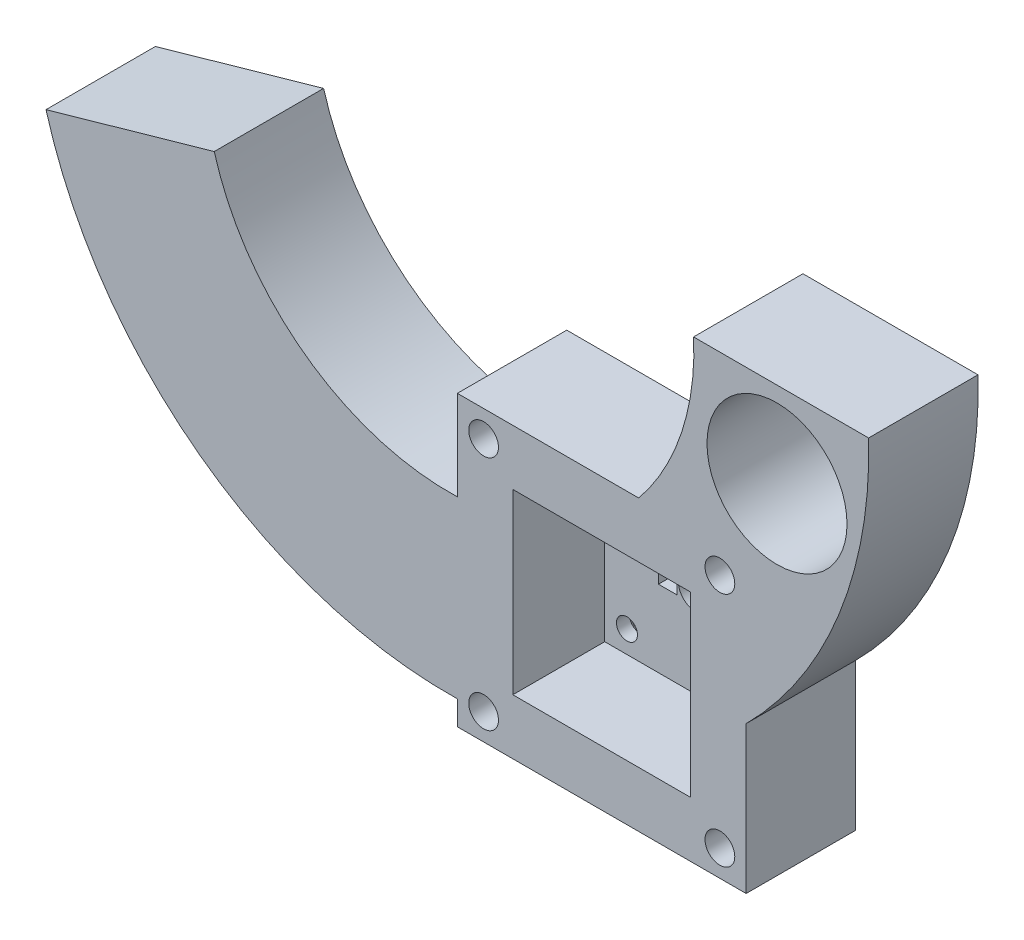
SolidWorks part; units mm, degrees
ref_plane "Plan de face" through (0, 0, 0) normal (0, 0, 1) x (1, 0, 0)
ref_plane "Plan de dessus" through (0, 0, 0) normal (0, 1, 0) x (1, 0, 0)
ref_plane "Plan de droite" through (0, 0, 0) normal (1, 0, 0) x (0, 0, -1)
sketch "Esquisse1" plane through (0, 0, 0) normal (0, 0, 1) x (1, 0, 0)
  line L0 (-16.5, 16.5) -> (16.5, -16.5) construction
  line L1 (-16.5, 16.5) -> (16.5, 16.5)
  line L2 (-16.5, 16.5) -> (-16.5, -16.5)
  line L3 (-16.5, -16.5) -> (16.5, -16.5)
  line L4 (16.5, 16.5) -> (16.5, -16.5)
  line L5 (-16.5, -16.5) -> (16.5, 16.5) construction
  line L11 (10.6664, -10.6664) -> (-10.6664, 10.6664) construction
  line L12 (10.6664, 10.6664) -> (-10.6664, -10.6664) construction
  point P4 (0, 0)
  point P5 (0, 0)
  dimension "D1" = 33
  dimension "D2" = 33
  dimension "D3" = 16.5
  dimension "D4" = 16.5
extrude "Boss.-Extru.1" add sketch "Esquisse1" along normal blind 12.5
sketch "Esquisse2" plane through (0, 0, 12.5) normal (0, 0, 1) x (1, 0, 0)
  line L0 (-16.5, 16.5) -> (16.5, -16.5) construction
  line L1 (-16.5, -16.5) -> (16.5, 16.5) construction
  line L2 (-10.16, 0) -> (10.16, 0) construction
  line L3 (10.16, -10.16) -> (-10.16, -10.16) construction
  line L4 (-16.5, 16.5) -> (-16.5, -16.5)
  line L5 (-16.5, -16.5) -> (16.5, -16.5)
  line L6 (16.5, -16.5) -> (16.5, 16.5)
  line L7 (16.5, 16.5) -> (-16.5, 16.5)
  line L8 (-16.5, 16.5) -> (-16.5, -16.5)
  line L9 (-16.5, -16.5) -> (16.5, -16.5)
  line L10 (16.5, -16.5) -> (16.5, 16.5)
  line L11 (16.5, 16.5) -> (-16.5, 16.5)
  line L12 (10.16, -10.16) -> (10.16, 10.16) construction
  line L13 (10.16, 10.16) -> (-10.16, 10.16) construction
  line L14 (-10.16, -10.16) -> (-10.16, 10.16) construction
  line L15 (10.16, -10.16) -> (-10.16, 10.16) construction
  line L16 (10.16, 10.16) -> (-10.16, -10.16) construction
  line L17 (10.16, -10.16) -> (-10.16, -10.16)
  line L18 (10.16, -10.16) -> (10.16, 10.16)
  line L19 (10.16, 10.16) -> (-10.16, 10.16)
  line L20 (-10.16, -10.16) -> (-10.16, 10.16)
  line L21 (10.16, -10.16) -> (-10.16, 10.16) construction
  line L22 (10.16, 10.16) -> (-10.16, -10.16) construction
  line L23 (-7.62, 8.82) -> (7.62, 8.82)
  line L24 (7.62, 8.82) -> (7.62, 6.42)
  line L25 (7.62, 6.42) -> (-7.62, 6.42)
  circle A0 centre (-7.62, 7.62) radius 1.2
  circle A1 centre (7.62, 7.62) radius 1.2
  circle A2 centre (7.62, -7.62) radius 1.2
  circle A3 centre (-7.62, -7.62) radius 1.2
  point P2 (0, 0)
  point P10 (7.62, 7.62)
  point P11 (-7.62, 7.62)
  point P16 (0, 0)
  dimension "D8" = 2.4
  dimension "D9" = 2.4
  dimension "D10" = 2.4
  dimension "D2" = 20.32
  dimension "D3" = 20.32
  dimension "D4" = 2.54
  dimension "D5" = 2.54
  dimension "D6" = 2.54
  dimension "D7" = 2.54
  dimension "D1" = 0
sketch "Esquisse3" plane through (0, 0, 12.5) normal (0, 0, 1) x (1, 0, 0)
  line L0 (-0.95, 1.7) -> (1.45, -1.7) construction
  line L1 (-4.02, 1.4) -> (-1.92, 1.4)
  line L2 (-4.02, 1.4) -> (-4.02, -1.4)
  line L3 (-4.02, -1.4) -> (-1.92, -1.4)
  line L4 (-1.92, 1.4) -> (-1.92, -1.4)
  line L5 (-0.95, 1.7) -> (1.45, 1.7)
  line L6 (-0.95, 1.7) -> (-0.95, -1.7)
  line L7 (-0.95, -1.7) -> (1.45, -1.7)
  line L8 (1.45, 1.7) -> (1.45, -1.7)
  line L9 (-0.95, -1.7) -> (1.45, 1.7) construction
  line L10 (-4.02, 1.4) -> (-1.92, -1.4) construction
  line L11 (-4.02, -1.4) -> (-1.92, 1.4) construction
  line L12 (10.16, -10.16) -> (10.16, 10.16) construction
  circle A0 centre (0.25, 0) radius 2
  point P8 (0.25, 0)
  point P9 (-2.97, 0)
  dimension "D7" = 4
  dimension "D1" = 3.22
  dimension "D2" = 9.91
  dimension "D3" = 2.8
  dimension "D4" = 2.1
  dimension "D5" = 3.4
  dimension "D6" = 2.4
extrude "Enlèv. mat.-Extru.1" cut sketch "Esquisse3" against normal through all contours L1 L4 L3 L2 | A0
sketch "Esquisse4" plane through (0, 0, 12.5) normal (0, 0, 1) x (1, 0, 0)
  line L0 (-16.5, 16.5) -> (16.5, -16.5) construction
  line L1 (5.8031, -5.8031) -> (-5.8031, -5.8031)
  line L2 (5.8031, -5.8031) -> (5.8031, 5.8031)
  line L3 (5.8031, 5.8031) -> (-5.8031, 5.8031)
  line L4 (-5.8031, -5.8031) -> (-5.8031, 5.8031)
  line L5 (5.8031, -5.8031) -> (-5.8031, 5.8031) construction
  line L6 (5.8031, 5.8031) -> (-5.8031, -5.8031) construction
  circle A0 centre (0.25, 0) radius 2 construction
  circle A1 centre (0.25, 0) radius 2
  point P0 (0, 0)
  dimension "D1" = 0.25
extrude "Enlèv. mat.-Extru.2" [suppressed] cut sketch "Esquisse4" against normal blind 12.5
extrude "Enlèv. mat.-Extru.3" cut sketch "Esquisse2" against normal through all contours A3 | A2 | A1 L23 A0 L25 | L24 A1
sketch "Esquisse5" plane through (0, 0, 12.5) normal (0, 0, 1) x (1, 0, 0)
  line L1 (10.16, -10.16) -> (-10.16, -10.16)
  line L2 (10.16, -10.16) -> (10.16, 10.16)
  line L3 (10.16, 10.16) -> (-10.16, 10.16)
  line L4 (-16.5, 16.5) -> (-16.5, -16.5)
  line L5 (-16.5, -16.5) -> (16.5, -16.5)
  line L6 (16.5, -16.5) -> (16.5, 16.5)
  line L7 (16.5, 16.5) -> (-16.5, 16.5)
  line L8 (-16.5, 16.5) -> (-16.5, -16.5)
  line L9 (-16.5, -16.5) -> (16.5, -16.5)
  line L10 (16.5, -16.5) -> (16.5, 16.5)
  line L11 (16.5, 16.5) -> (-16.5, 16.5)
  line L12 (-10.16, -10.16) -> (-10.16, 10.16)
  line L13 (10.16, -10.16) -> (-10.16, 10.16) construction
  line L14 (10.16, 10.16) -> (-10.16, -10.16) construction
  point P2 (0, 0)
  dimension "D2" = 20.32
  dimension "D3" = 20.32
  dimension "D1" = 0
extrude "Enlèv. mat.-Extru.5" cut sketch "Esquisse5" against normal blind 10.5 contours L3 L12 L1 L2
sketch "Esquisse6" plane through (0, 0, 12.5) normal (0, 0, 1) x (1, 0, 0)
  line L0 (10.16, 0) -> (-10.16, 0) construction
  line L1 (10.16, -10.16) -> (10.16, 10.16) construction
  line L2 (-10.16, -10.16) -> (-10.16, 10.16) construction
  line L3 (-16.5, 0) -> (16.5, 0) construction
  line L4 (-16.5, 16.5) -> (-16.5, -16.5)
  line L5 (-16.5, -16.5) -> (16.5, -16.5)
  line L6 (16.5, -16.5) -> (16.5, 16.5)
  line L7 (16.5, 16.5) -> (-16.5, 16.5)
  line L8 (-16.5, 16.5) -> (-16.5, -16.5)
  line L9 (-16.5, -16.5) -> (16.5, -16.5)
  line L10 (16.5, -16.5) -> (16.5, 16.5)
  line L11 (16.5, 16.5) -> (-16.5, 16.5)
  circle A0 centre (13.5, -13.5) radius 1.5
  circle A1 centre (-13.5, -13.5) radius 1.5
  circle A4 centre (13.5, 13.5) radius 1.5
  circle A5 centre (-13.5, 13.5) radius 1.5
  point P21 (-13.5, 13.5)
  point P22 (13.5, 13.5)
  dimension "D6" = 3
  dimension "D7" = 3
  dimension "D2" = 3
  dimension "D3" = 3
  dimension "D4" = 3
  dimension "D5" = 3
  dimension "D1" = 0
sketch "Esquisse8" plane through (0, 0, 0) normal (0, 0, -1) x (-1, 0, 0)
  line L0 (-10.4912, 35.5773) -> (-30.4912, 35.5773)
  line L1 (44.2787, 26.5367) -> (63.502, 21.0704)
  line L3 (44.2787, 26.5367) -> (17.4088, 34.1773) construction
  line L4 (-4.2218, 16.5) -> (-16.5, 16.5)
  line L5 (-16.5, 16.5) -> (16.5, 16.5) construction
  line L6 (-16.5, 16.5) -> (-16.5, 0.3164)
  line L7 (-16.5, -16.5) -> (-16.5, 16.5) construction
  line L8 (16.5, -13.7345) -> (16.5, 6.257)
  line L9 (16.5, 16.5) -> (16.5, -16.5) construction
  line L10 (-20.024, 25.8144) -> (17.4088, 34.1773) construction
  line L11 (17.4088, 34.1773) -> (43.3677, 5.941) construction
  line L12 (17.4088, 34.1773) -> (0, 0) construction
  circle A3 centre (-20.024, 25.8144) radius 8
  arc A4 (-20.9213, 35.5773) -> (54.3019, 23.6865) centre (17.4088, 34.1773) ccw construction
  arc A5 (-30.4912, 35.5773) -> (-16.5, 0.3164) centre (17.4088, 34.1773) ccw
  arc A6 (-10.4912, 35.5773) -> (-4.2218, 16.5) centre (17.4088, 34.1773) ccw
  arc A7 (16.5, 6.257) -> (44.2787, 26.5367) centre (17.4088, 34.1773) ccw
  arc A8 (16.5, -13.7345) -> (63.502, 21.0704) centre (17.4088, 34.1773) ccw
  dimension "D1" = 9.7629
  dimension "D2" = 16
  dimension "D3" = 120
extrude "Boss.-Extru.4" add sketch "Esquisse8" against normal up to surface (12.5 mm away)
hole_wizard "Dégagement M31" positions "Esquisse3D1" profile "Esquisse7" hole size "M3" standard "Ansi Metric" end condition through all
sketch3d "Esquisse3D1"
  point P0 (-13.5, 13.5, 12.5)
  point P3 (13.5, 13.5, 12.5)
  point P6 (13.5, -13.5, 12.5)
  point P9 (-13.5, -13.5, 12.5)
sketch "Esquisse7" plane through (-13.5, 13.5, 12.5) normal (1, 0, 0) x (0, -1, 0)
  line L0 (0, 0) -> (0, 12.5)
  line L1 (0, 12.5) -> (1.7, 12.5)
  line L2 (1.7, 12.5) -> (1.7, 0)
  line L5 (1.7, 0) -> (0, 0)
  line L11 (0, -6.35) -> (0, 107.95) construction
  dimension "Diamètre du perçage jusqu'au prochain" = 3.4
  dimension "Profondeur du perçage jusqu'au prochain" = 12.5
ref_plane "Plan1" through (-10.16, 10.16, 12.5) normal (0, 1, 0) x (1, 0, 0)
chamfer "Chanfrein1" distance 1 angle 45 4 edges at (15.2, 13.5, 0) (15.2, -13.5, 0) (-11.8, -13.5, 0) (-11.8, 13.5, 0)
chamfer "Chanfrein2" distance 0.5 angle 45 2 edges at (8.82, -7.62, 0) (-6.42, -7.62, 0)
